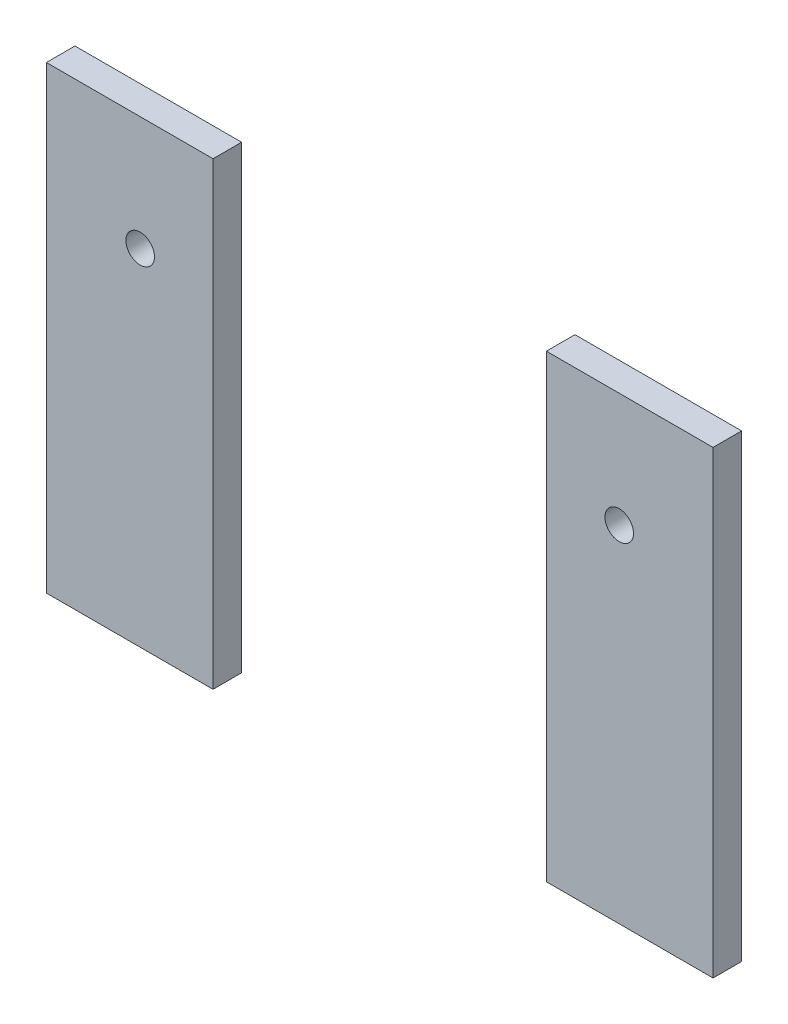
SolidWorks part; units mm, degrees
material "6061-T6 (SS)"
ref_plane "Front Plane" through (0, 0, 0) normal (0, 0, 1) x (1, 0, 0)
ref_plane "Top Plane" through (0, 0, 0) normal (0, 1, 0) x (1, 0, 0)
ref_plane "Right Plane" through (0, 0, 0) normal (1, 0, 0) x (0, 0, -1)
sketch "Sketch1" plane through (0, 0, 0) normal (0, 0, 1) x (1, 0, 0)
  line L1 (70, -102.5) -> (-70, -102.5)
  line L2 (70, -102.5) -> (70, 62.5)
  line L3 (70, 62.5) -> (-70, 62.5)
  line L4 (-70, -102.5) -> (-70, 62.5)
  point P0 (0, 0)
extrude "Boss-Extrude1" add sketch "Sketch1" along normal blind 6
fillet "Fillet1" radius 10 2 edges at (-70, 62.5, 3) (70, 62.5, 3)
sketch "Sketch9" plane through (0, 0, 6) normal (0, 0, 1) x (1, 0, 0)
  circle A0 centre (50.3, 30) radius 3
  circle A1 centre (50.3, -30) radius 3
  circle A2 centre (-50.3, 30) radius 3
  circle A3 centre (-50.3, -30) radius 3
extrude "Cut-Extrude1" cut sketch "Sketch9" against normal blind 10
sketch "Sketch10" plane through (0, 0, 6) normal (0, 0, 1) x (1, 0, 0)
  line L1 (-35, -117.2122) -> (35, -117.2122)
  line L2 (-35, -117.2122) -> (-35, 78.6292)
  line L3 (-35, 78.6292) -> (35, 78.6292)
  line L4 (35, -117.2122) -> (35, 78.6292)
  point P4 (0, 0)
  point P5 (0, 0)
  point P6 (0, 0)
  point P7 (0, 0)
extrude "Cut-Extrude2" cut sketch "Sketch10" against normal blind 10
sketch "Sketch11" plane through (0, 0, 6) normal (0, 0, 1) x (1, 0, 0)
  line L1 (-84.7171, -6) -> (88.0578, -6)
  line L2 (-84.7171, -6) -> (-84.7171, 68.1692)
  line L3 (-84.7171, 68.1692) -> (88.0578, 68.1692)
  line L4 (88.0578, -6) -> (88.0578, 68.1692)
  point P4 (25.8782, -14.9206)
  point P5 (0, 0)
  point P6 (0, 0)
extrude "Cut-Extrude4" cut sketch "Sketch11" against normal blind 10
